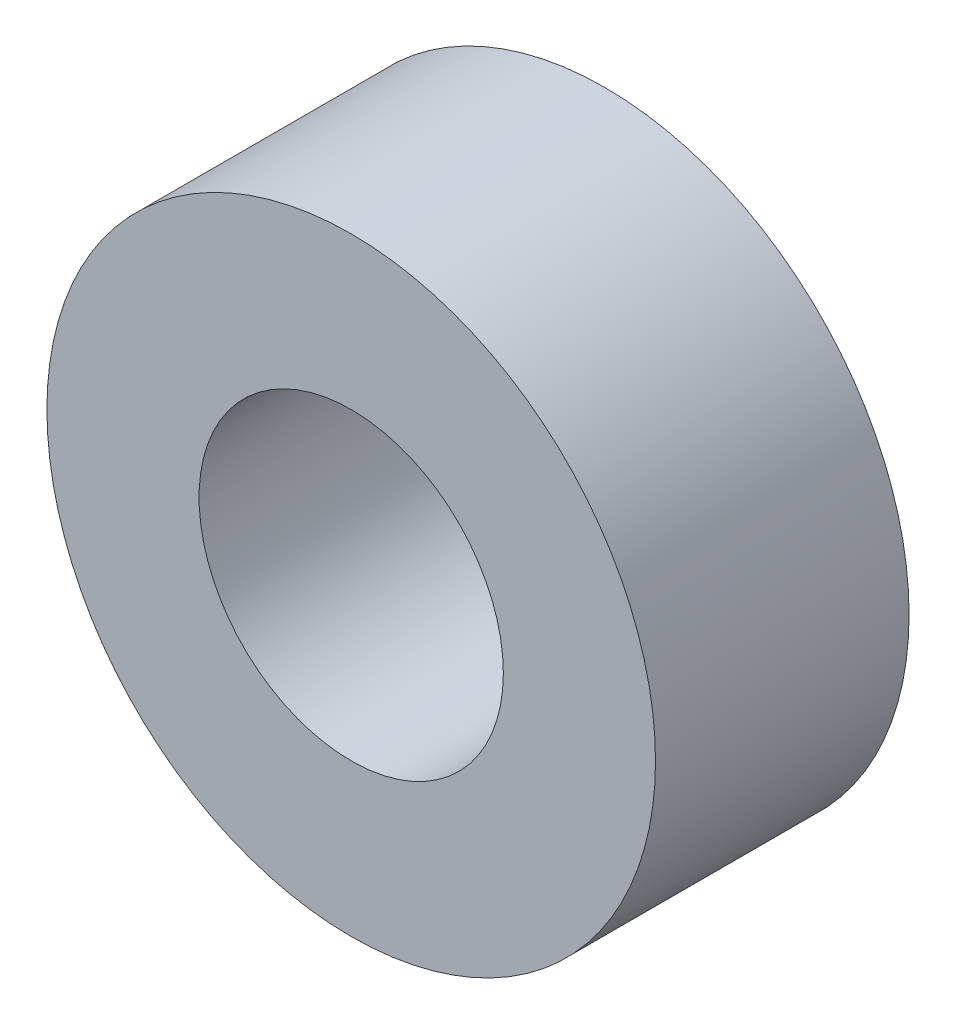
SolidWorks part; units mm, degrees
ref_plane "前视基准面" through (0, 0, 0) normal (0, 0, 1) x (1, 0, 0)
ref_plane "上视基准面" through (0, 0, 0) normal (0, 1, 0) x (1, 0, 0)
ref_plane "右视基准面" through (0, 0, 0) normal (1, 0, 0) x (0, 0, -1)
sketch "草图1" plane through (0, 0, 0) normal (0, 0, 1) x (1, 0, 0)
  circle A0 centre (0, 0) radius 1.5
  circle A1 centre (0, 0) radius 3
extrude "凸台-拉伸1" add sketch "草图1" along normal blind 2.5
